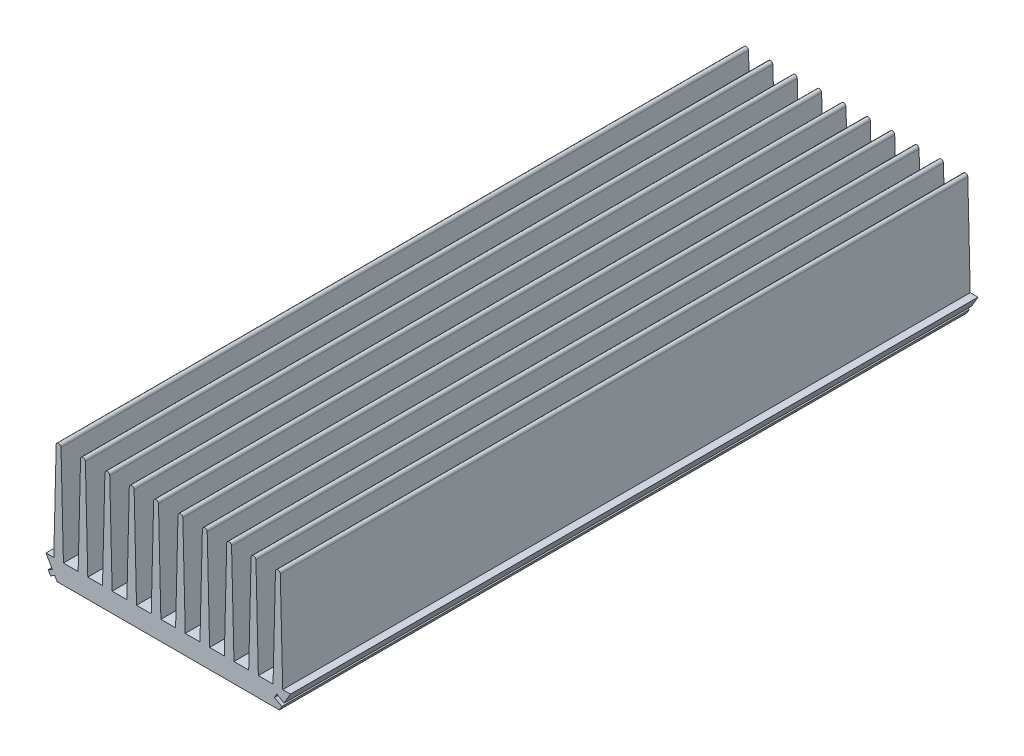
SolidWorks part; units mm, degrees
ref_plane "Plano frontal" through (0, 0, 0) normal (0, 0, 1) x (1, 0, 0)
ref_plane "Plano superior" through (0, 0, 0) normal (0, 1, 0) x (1, 0, 0)
ref_plane "Plano direito" through (0, 0, 0) normal (1, 0, 0) x (0, 0, -1)
sketch "Esboço1" plane through (0, 0, 0) normal (0, 0, 1) x (1, 0, 0)
  line L3 (0, 0) -> (-115.1, 0)
  line L102 (-70.7, 8) -> (-64.6, 8)
  line L103 (-80.8, 8) -> (-74.7, 8)
  line L104 (-84.8, 8) -> (-90.9, 8)
  line L114 (-60.6, 8) -> (-54.5, 8)
  line L115 (-57.55, 0) -> (-57.55, 50) construction
  line L116 (-129.2406, 50) -> (13.8512, 50) construction
  line L146 (-84.8, 8) -> (-83.8, 49)
  line L147 (-81.8, 49) -> (-80.8, 8)
  line L148 (-83.8, 49) -> (-81.8, 49) construction
  line L149 (-90.9, 8) -> (-91.9, 49)
  line L150 (-93.9, 49) -> (-94.9, 8)
  line L151 (-82.8, 49) -> (-82.8, 0) construction
  line L152 (-94.9, 8) -> (-101, 8)
  line L153 (-101, 8) -> (-102, 49)
  line L154 (-104, 49) -> (-105, 8)
  line L155 (-74.7, 8) -> (-73.7, 49)
  line L156 (-71.7, 49) -> (-70.7, 8)
  line L161 (-73.7, 49) -> (-71.7, 49) construction
  line L162 (-64.6, 8) -> (-63.6, 49)
  line L163 (-105, 8) -> (-111.1, 8)
  line L164 (-63.6, 49) -> (-61.6, 49) construction
  line L165 (-61.6, 49) -> (-60.6, 8)
  line L167 (-111.1, 8) -> (-112.1, 49)
  line L168 (-115.1, 0) -> (-115.1, 8)
  line L169 (-115.1, 8) -> (-111.1, 8) construction
  line L170 (-91.9, 49) -> (-93.9, 49) construction
  line L171 (-102, 49) -> (-104, 49) construction
  line L172 (-112.1, 49) -> (-114.1, 49) construction
  line L173 (-80.8, 8) -> (-82.8, 8) construction
  line L174 (-82.8, 8) -> (-84.8, 8) construction
  line L175 (-115.1, 8) -> (-114.1, 49)
  line L176 (-32.3, 8) -> (-30.3, 8) construction
  line L177 (-34.3, 8) -> (-32.3, 8) construction
  line L178 (-3, 49) -> (-1, 49) construction
  line L179 (-13.1, 49) -> (-11.1, 49) construction
  line L180 (-23.2, 49) -> (-21.2, 49) construction
  line L181 (0, 8) -> (-4, 8) construction
  line L182 (-51.5, 49) -> (-53.5, 49) construction
  line L183 (-41.4, 49) -> (-43.4, 49) construction
  line L184 (-32.3, 49) -> (-32.3, 0) construction
  line L185 (-31.3, 49) -> (-33.3, 49) construction
  line L186 (0, 8) -> (-1, 49)
  line L187 (0, 0) -> (0, 8)
  line L188 (-4, 8) -> (-3, 49)
  line L189 (-53.5, 49) -> (-54.5, 8)
  line L190 (-10.1, 8) -> (-4, 8)
  line L191 (-50.5, 8) -> (-51.5, 49)
  line L192 (-43.4, 49) -> (-44.4, 8)
  line L193 (-40.4, 8) -> (-41.4, 49)
  line L194 (-11.1, 49) -> (-10.1, 8)
  line L195 (-14.1, 8) -> (-13.1, 49)
  line L196 (-20.2, 8) -> (-14.1, 8)
  line L197 (-21.2, 49) -> (-20.2, 8)
  line L198 (-24.2, 8) -> (-23.2, 49)
  line L199 (-33.3, 49) -> (-34.3, 8)
  line L200 (-30.3, 8) -> (-31.3, 49)
  line L201 (-30.3, 8) -> (-24.2, 8)
  line L202 (-34.3, 8) -> (-40.4, 8)
  line L203 (-44.4, 8) -> (-50.5, 8)
  arc A4 (-83.8, 49) -> (-81.8, 49) centre (-82.8, 49) cw
  arc A6 (-73.7, 49) -> (-71.7, 49) centre (-72.7, 49) cw
  arc A8 (-63.6, 49) -> (-61.6, 49) centre (-62.6, 49) cw
  arc A20 (-91.9, 49) -> (-93.9, 49) centre (-92.9, 49) ccw
  arc A21 (-104, 49) -> (-102, 49) centre (-103, 49) cw
  arc A22 (-114.1, 49) -> (-112.1, 49) centre (-113.1, 49) cw
  arc A23 (-1, 49) -> (-3, 49) centre (-2, 49) ccw
  arc A24 (-11.1, 49) -> (-13.1, 49) centre (-12.1, 49) ccw
  arc A25 (-23.2, 49) -> (-21.2, 49) centre (-22.2, 49) cw
  arc A26 (-51.5, 49) -> (-53.5, 49) centre (-52.5, 49) ccw
  arc A27 (-41.4, 49) -> (-43.4, 49) centre (-42.4, 49) ccw
  arc A28 (-31.3, 49) -> (-33.3, 49) centre (-32.3, 49) ccw
  point P13 (-57.55, 8)
  dimension "D2" = 1
  dimension "D3" = 8
  dimension "D4" = 6.1
  dimension "D8" = 50
  dimension "D14" = 8.1
extrude "Ressalto-extrusão1" add sketch "Esboço1" along normal blind 285
sketch "Esboço2" plane through (0, 0, 285) normal (0, 0, 1) x (1, 0, 0)
  line L0 (-11.4962, 0) -> (0, 0)
  line L1 (-115.1, 0) -> (0, 0) construction
  line L2 (0, 0) -> (0, 52.2476)
  line L3 (0, 52.2476) -> (-6.8774, 52.2476)
  line L4 (-6.8774, 52.2476) -> (-6.8774, 8)
  line L5 (-4, 8) -> (-10.1, 8) construction
  line L6 (-6.3, 9) -> (-9.4962, 3.4641) construction
  line L7 (-6.8774, 8) -> (-9.4962, 3.4641)
  line L8 (-9.4962, 3.4641) -> (-12.5272, 5.2141)
  line L9 (-12.5272, 5.2141) -> (-13.5272, 3.4821)
  line L10 (-13.5272, 3.4821) -> (-10.4962, 1.7321)
  line L11 (-10.4962, 1.7321) -> (-11.4962, 0)
  line L12 (-103.6038, 0) -> (-116.9816, 0)
  line L13 (-116.9816, 0) -> (-116.9816, 53.4331)
  line L14 (-116.9816, 53.4331) -> (-108.2226, 53.4331)
  line L15 (-108.2226, 53.4331) -> (-108.2226, 8)
  line L16 (-105, 8) -> (-111.1, 8) construction
  line L17 (-108.2226, 8) -> (-105.6038, 3.4641)
  line L18 (-105.6038, 3.4641) -> (-107.3359, 2.4641)
  line L19 (-107.3359, 2.4641) -> (-106.3359, 0.7321)
  line L20 (-106.3359, 0.7321) -> (-104.6038, 1.7321)
  line L21 (-104.6038, 1.7321) -> (-103.6038, 0)
  line L22 (-105.6038, 3.4641) -> (-108.8, 9) construction
  line L24 (-10.4962, 1.7321) -> (-11.4962, 0) construction
  line L25 (-103.6038, 0) -> (-104.6038, 1.7321) construction
  point P35 (-108.2226, 8)
  point P38 (-103.5184, 0)
  point P39 (-103.7621, 0)
  point P40 (-103.6038, 0)
  point P42 (-11.4962, 0)
extrude "Corte-extrusão1" cut sketch "Esboço2" against normal through all both and the other way through all
